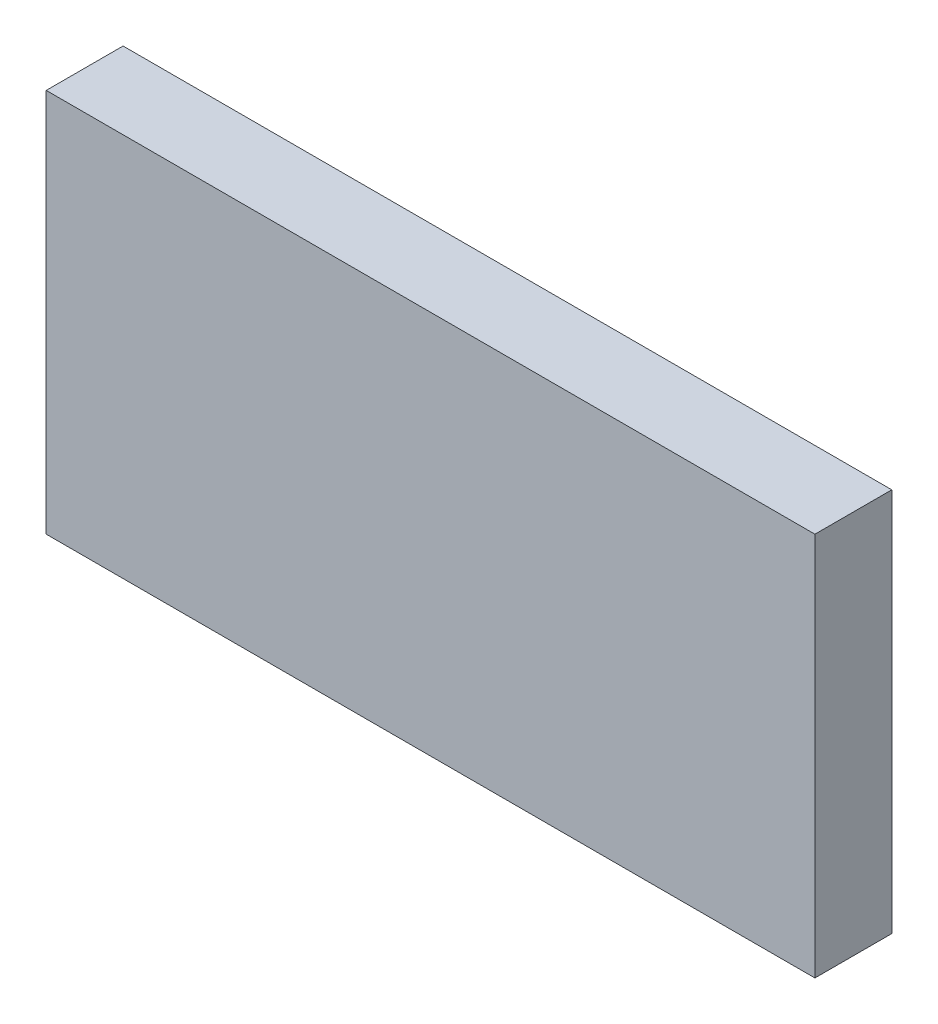
SolidWorks part; units mm, degrees
material "Cedar"
ref_plane "Front Plane" through (0, 0, 0) normal (0, 0, 1) x (1, 0, 0)
ref_plane "Top Plane" through (0, 0, 0) normal (0, 1, 0) x (1, 0, 0)
ref_plane "Right Plane" through (0, 0, 0) normal (1, 0, 0) x (0, 0, -1)
sketch "Sketch1" plane through (0, 0, 0) normal (0, 0, 1) x (1, 0, 0)
  line L1 (-15, -7.5) -> (15, -7.5)
  line L2 (-15, -7.5) -> (-15, 7.5)
  line L3 (-15, 7.5) -> (15, 7.5)
  line L4 (15, -7.5) -> (15, 7.5)
  line L5 (-15, -7.5) -> (15, 7.5) construction
  line L6 (-15, 7.5) -> (15, -7.5) construction
  point P0 (0, 0)
  dimension "D1" = 30
  dimension "D2" = 15
extrude "Boss-Extrude1" add sketch "Sketch1" along normal blind 3
